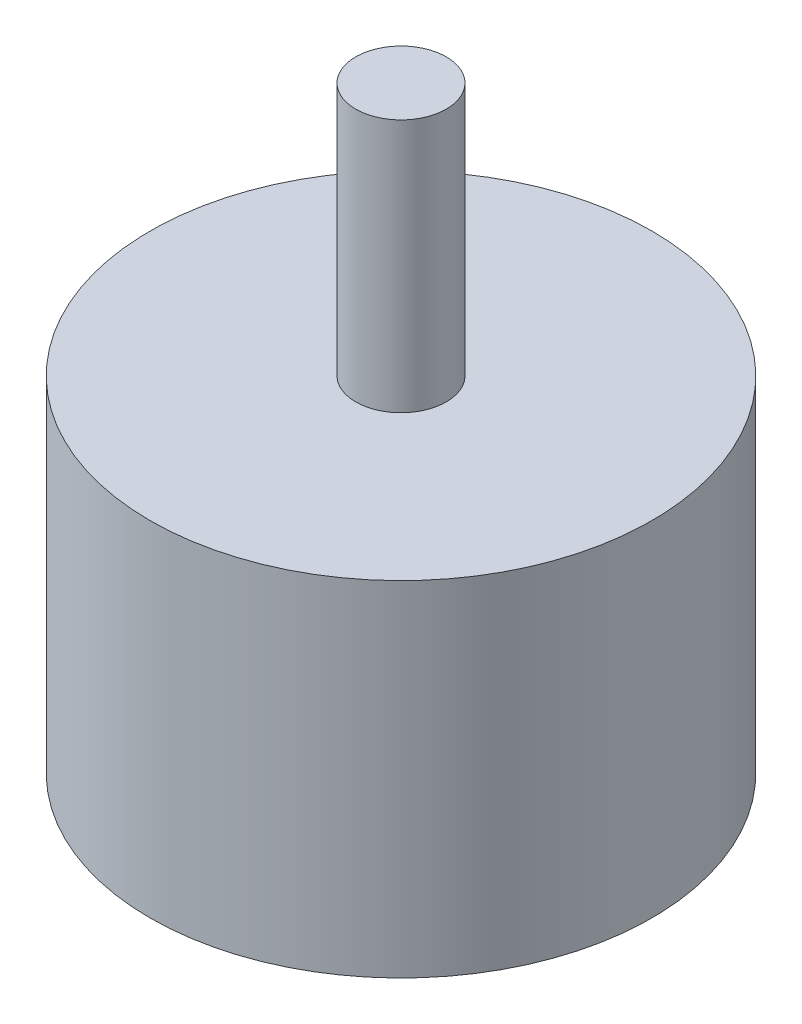
SolidWorks part; units mm, degrees
ref_plane "Front Plane" through (0, 0, 0) normal (0, 0, 1) x (1, 0, 0)
ref_plane "Top Plane" through (0, 0, 0) normal (0, 1, 0) x (1, 0, 0)
ref_plane "Right Plane" through (0, 0, 0) normal (1, 0, 0) x (0, 0, -1)
sketch "Sketch1" plane through (0, 0, 0) normal (0, 1, 0) x (1, 0, 0)
  circle A0 centre (0, 0) radius 13.85
  dimension "D1" = 27.7
extrude "Boss-Extrude1" add sketch "Sketch1" along normal blind 19
sketch "Sketch2" plane through (0, 19, 0) normal (0, 1, 0) x (1, 0, 0)
  circle A0 centre (0, 0) radius 2.5
  dimension "D1" = 5
extrude "Boss-Extrude2" add sketch "Sketch2" along normal blind 14
sketch "Sketch3" plane through (0, 0, 0) normal (0, -1, 0) x (1, 0, 0)
  circle A0 centre (0, 0) radius 8
  circle A1 centre (0, 0) radius 9.5
  point P4 (0, 8)
  point P5 (0, -8)
  point P6 (9.5, 0)
  point P7 (-9.5, 0)
  dimension "D1" = 16
  dimension "D2" = 19
hole_wizard "M3x0.5 Tapped Hole1" positions "Sketch4" profile "Sketch5" tap size "M3x0.5" standard "ANSI Metric"
sketch "Sketch4" plane through (0, 0, 0) normal (0, -1, 0) x (-1, 0, 0)
  point P0 (0, -8)
  point P3 (9.5, 0)
  point P6 (0, 8)
  point P9 (-9.5, 0)
sketch "Sketch5" plane through (0, 0, 8) normal (1, 0, 0) x (0, 0, -1)
  line L0 (0, 0) -> (0, 8.2511)
  line L1 (0, 8.2511) -> (1.25, 7.5)
  line L2 (1.25, 7.5) -> (1.25, 0)
  line L5 (1.25, 0) -> (0, 0)
  line L10 (0, 8.2511) -> (-1.25, 7.5) construction
  line L11 (0, -6.35) -> (0, 107.95) construction
  dimension "Tap Drill Dia." = 2.5
  dimension "Tap Drill Depth" = 7.5
  dimension "Drill Angle" = 118
cosmetic thread "Hole Thread1" parameters "D1"=6, "D2"=3
cosmetic thread "Hole Thread2" parameters "D1"=6, "D2"=3
cosmetic thread "Hole Thread3" parameters "D1"=6, "D2"=3
cosmetic thread "Hole Thread4" parameters "D1"=6, "D2"=3
